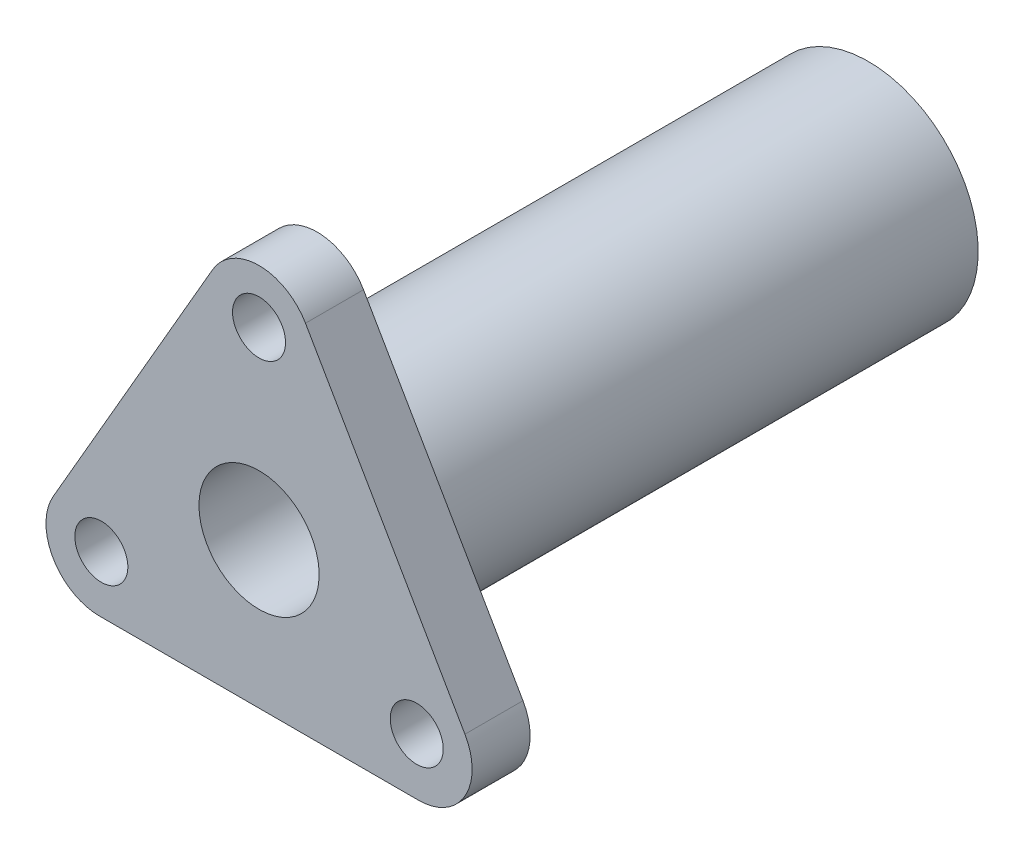
SolidWorks part; units mm, degrees
ref_plane "Front Plane" through (0, 0, 0) normal (0, 0, 1) x (1, 0, 0)
ref_plane "Top Plane" through (0, 0, 0) normal (0, 1, 0) x (1, 0, 0)
ref_plane "Right Plane" through (0, 0, 0) normal (1, 0, 0) x (0, 0, -1)
sketch "Sketch1" plane through (0, 0, 0) normal (0, 0, 1) x (1, 0, 0)
  line L0 (0, 23.094) -> (20, -11.547)
  line L1 (20, -11.547) -> (-20, -11.547)
  line L2 (-20, -11.547) -> (0, 23.094)
  line L3 (0, 23.094) -> (0, -17.3205) construction
  line L4 (20, -11.547) -> (-10, 5.7735) construction
  line L5 (-20, -11.547) -> (10, 5.7735) construction
  dimension "D1" = 60
  dimension "D2" = 60
  dimension "D3" = 40
  dimension "D4" = 20
  dimension "D5" = 17.3205
extrude "Boss-Extrude1" add sketch "Sketch1" along normal blind 4.6
hole_wizard "M5x0.8 Tapped Hole1" positions "Sketch6" profile "Sketch5" tap size "M5x0.8" standard "ANSI Metric" end condition through all
sketch "Sketch6" plane through (0, 0, 0) normal (0, 0, -1) x (-1, 0, 0)
  line L1 (0, 14.594) -> (-12.5, -7.0566) construction
  line L2 (-12.5, -7.0566) -> (12.5, -7.0566) construction
  line L3 (12.5, -7.0566) -> (0, 14.594) construction
  line L7 (20, -11.547) -> (-20, -11.547) construction
  line L9 (-12.5, -7.0566) -> (-20, -11.547) construction
  point P0 (0, 14.594)
  point P2 (-12.5, -7.0566)
  point P4 (12.5, -7.0566)
  dimension "D1" = 25
  dimension "D2" = 25
  dimension "D3" = 25
  dimension "D4" = 7.5
  dimension "D5" = 8.5
sketch "Sketch5" plane through (0, 14.594, 0) normal (1, 0, 0) x (0, 1, 0)
  line L0 (0, 0) -> (0, 4.6)
  line L1 (0, 4.6) -> (2.1, 4.6)
  line L2 (2.1, 4.6) -> (2.1, 0)
  line L5 (2.1, 0) -> (0, 0)
  line L11 (0, -6.35) -> (0, 107.95) construction
  dimension "Thru Tap Drill Dia." = 4.2
  dimension "Thru Tap Drill Depth" = 4.6
cosmetic thread "Hole Thread1" parameters "D2"=5
cosmetic thread "Hole Thread2" parameters "D2"=5
cosmetic thread "Hole Thread3" parameters "D2"=5
fillet "Fillet1" radius 4.25 3 edges at (0, 23.094, 2.3) (-20, -11.547, 2.3) (20, -11.547, 2.3)
sketch "Sketch9" plane through (0, 0, 0) normal (0, 0, -1) x (-1, 0, 0)
  circle A0 centre (0, 0) radius 8.7
  dimension "D1" = 17.4
extrude "Boss-Extrude2" add sketch "Sketch9" along normal blind 43.7
sketch "Sketch10" plane through (0, 0, -43.7) normal (0, 0, -1) x (-1, 0, 0)
  circle A0 centre (0, 0) radius 4.7625
  dimension "D1" = 9.525
extrude "Cut-Extrude1" cut sketch "Sketch10" against normal blind 48.3
